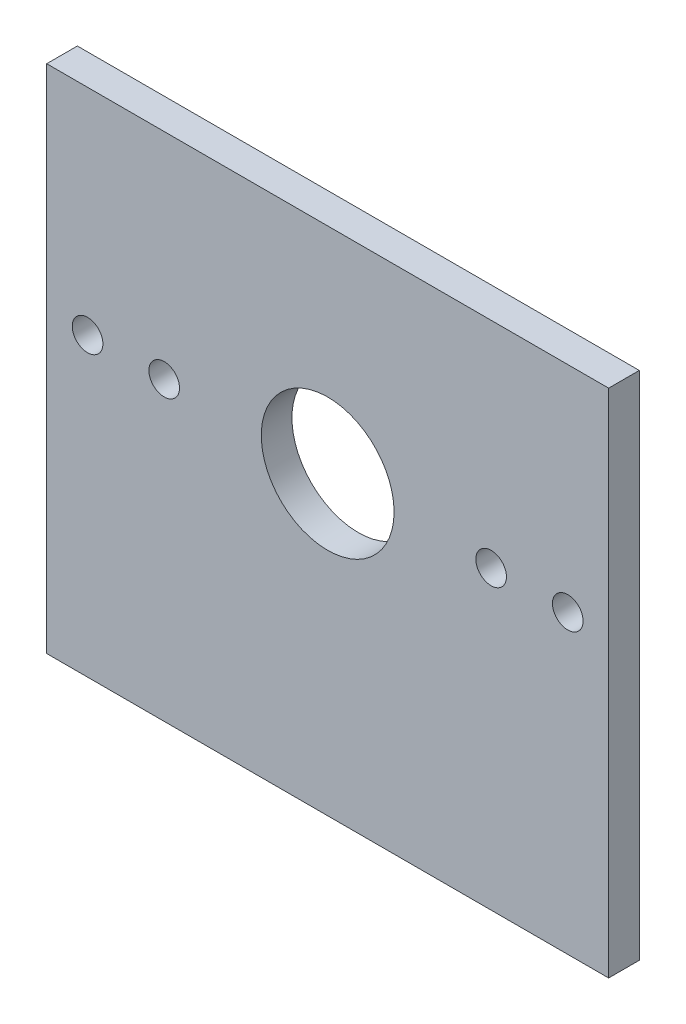
SolidWorks part; units mm, degrees
ref_plane "Plan de face" through (0, 0, 0) normal (0, 0, 1) x (1, 0, 0)
ref_plane "Plan de dessus" through (0, 0, 0) normal (0, 1, 0) x (1, 0, 0)
ref_plane "Plan de droite" through (0, 0, 0) normal (1, 0, 0) x (0, 0, -1)
sketch "Esquisse1" plane through (0, 0, 0) normal (0, 0, 1) x (1, 0, 0)
  line L0 (-23.5, 4) -> (23.5, 4) construction
  line L1 (-27.5, -25) -> (27.5, -25)
  line L2 (-27.5, -25) -> (-27.5, 25)
  line L3 (-27.5, 25) -> (27.5, 25)
  line L4 (27.5, -25) -> (27.5, 25)
  circle A0 centre (0, 4) radius 6.5
  circle A1 centre (16, 4) radius 1.5
  circle A2 centre (23.5, 4) radius 1.5
  circle A3 centre (-16, 4) radius 1.5
  circle A4 centre (-23.5, 4) radius 1.5
  dimension "D5" = 13
  dimension "D9" = 3
  dimension "D10" = 3
  dimension "D11" = 3
  dimension "D12" = 3
  dimension "D1" = 50
  dimension "D2" = 55
  dimension "D3" = 25
  dimension "D4" = 27.5
  dimension "D6" = 29
  dimension "D7" = 16
  dimension "D8" = 7.5
  dimension "D13" = 7.5
  dimension "D14" = 16
extrude "Boss.-Extru.1" add sketch "Esquisse1" along normal blind 3
